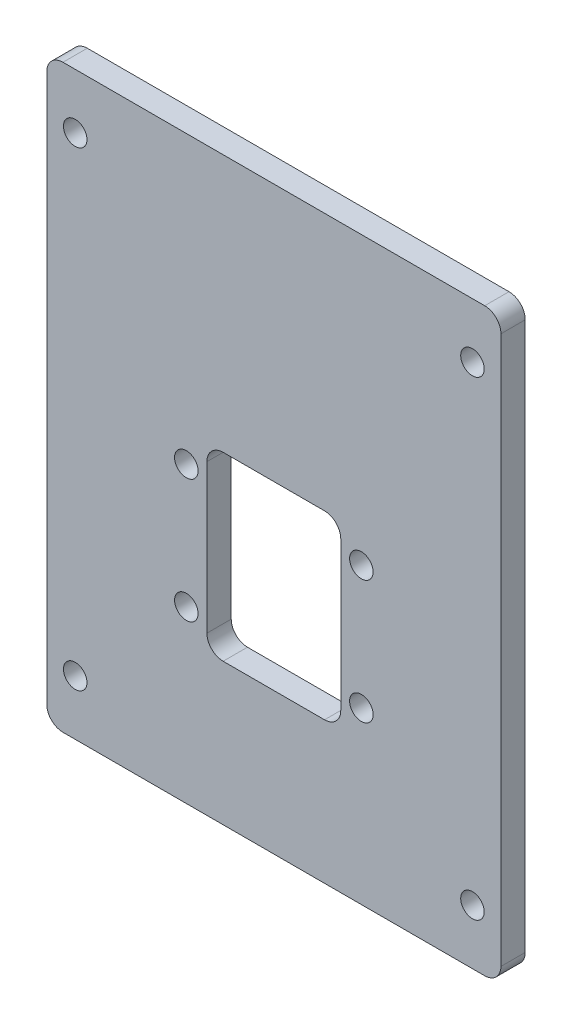
SolidWorks part; units mm, degrees
ref_plane "Front Plane" through (0, 0, 0) normal (0, 0, 1) x (1, 0, 0)
ref_plane "Top Plane" through (0, 0, 0) normal (0, 1, 0) x (1, 0, 0)
ref_plane "Right Plane" through (0, 0, 0) normal (1, 0, 0) x (0, 0, -1)
sketch "Sketch1" plane through (0, 0, 0) normal (0, 0, 1) x (1, 0, 0)
  line L0 (-10.335, -10.16) -> (10.335, -10.16) construction
  line L1 (-28.01, 42.95) -> (28.01, 42.95)
  line L2 (-28.01, 42.95) -> (-28.01, -28.63)
  line L3 (-28.01, -28.63) -> (28.01, -28.63)
  line L4 (28.01, 42.95) -> (28.01, -28.63)
  line L5 (-8.255, 11.16) -> (8.255, 11.16)
  line L6 (-8.255, 11.16) -> (-8.255, -11.16)
  line L7 (-8.255, -11.16) -> (8.255, -11.16)
  line L8 (8.255, 11.16) -> (8.255, -11.16)
  line L9 (10.335, 10.16) -> (-10.335, 10.16) construction
  line L10 (8.255, 0) -> (13.335, 0) construction
  line L13 (10.795, -7.62) -> (10.795, 7.62) construction
  line L14 (13.335, -7.16) -> (13.335, 7.16) construction
  line L15 (-10.795, -7.62) -> (-10.795, 7.62) construction
  line L16 (-13.335, 0) -> (-8.255, 0) construction
  line L17 (-13.335, 7.16) -> (-13.335, -7.16) construction
  line L18 (-28.01, -28.63) -> (28.01, -28.63) construction
  line L19 (28.01, -28.63) -> (28.01, 42.95) construction
  line L20 (28.01, 42.95) -> (-28.01, 42.95) construction
  line L21 (-28.01, 42.95) -> (-28.01, -28.63) construction
  circle A0 centre (-10.795, 7.62) radius 1.45 construction
  circle A1 centre (-10.795, -7.62) radius 1.45 construction
  circle A2 centre (10.795, 7.62) radius 1.45 construction
  circle A3 centre (10.795, -7.62) radius 1.45 construction
  circle A4 centre (-10.795, -7.62) radius 1.45
  circle A5 centre (-10.795, 7.62) radius 1.45
  circle A6 centre (10.795, 7.62) radius 1.45
  circle A7 centre (10.795, -7.62) radius 1.45
  circle A8 centre (-24.5, 36.16) radius 1.45 construction
  circle A9 centre (24.5, -21.84) radius 1.45
  circle A10 centre (24.5, -21.84) radius 1.45
  circle A11 centre (-24.5, -21.84) radius 1.45 construction
  circle A12 centre (-24.5, 36.16) radius 1.45
  circle A13 centre (-24.5, -21.84) radius 1.45
  circle A14 centre (24.5, 36.16) radius 1.45 construction
  circle A15 centre (24.5, 36.16) radius 1.45
  point P19 (10.795, 0)
  point P22 (-10.795, 0)
  dimension "D1" = 1
  dimension "D2" = 1
  dimension "D3" = 0
extrude "Boss-Extrude1" add sketch "Sketch1" along normal blind 3
fillet "Fillet1" radius 2 8 edges at (8.255, -11.16, 1.5) (8.255, 11.16, 1.5) (-8.255, 11.16, 1.5) (-8.255, -11.16, 1.5) (-28.01, 42.95, 1.5) (28.01, 42.95, 1.5) (-28.01, -28.63, 1.5) (28.01, -28.63, 1.5)
